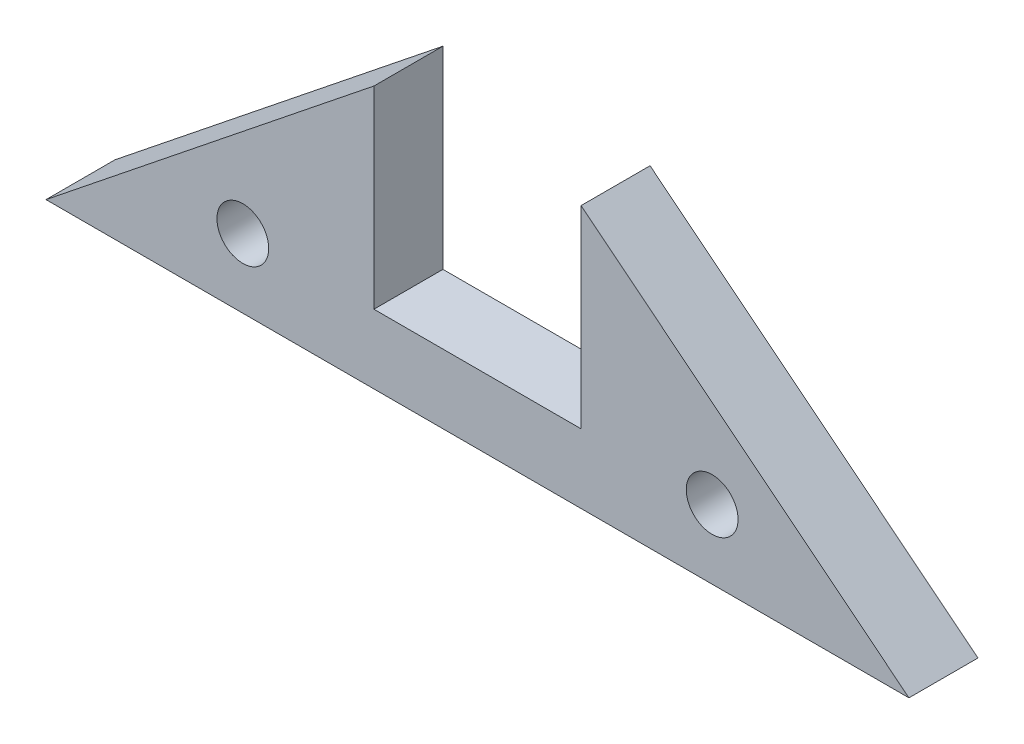
SolidWorks part; units mm, degrees
material "ABS"
ref_plane "Front" through (0, 0, 0) normal (0, 0, 1) x (1, 0, 0)
ref_plane "Top" through (0, 0, 0) normal (0, 1, 0) x (1, 0, 0)
ref_plane "Right" through (0, 0, 0) normal (1, 0, 0) x (0, 0, -1)
sketch "Sketch1" plane through (0, 0, 0) normal (0, 0, 1) x (1, 0, 0)
  line L0 (0, 0) -> (63.5, 0)
  line L1 (63.5, 0) -> (31.75, 25.4)
  line L2 (31.75, 25.4) -> (0, 0)
  point P6 (31.75, 0)
  dimension "D1" = 63.5
  dimension "D2" = 25.4
extrude "Boss-Extrude1" add sketch "Sketch1" along normal blind 5.08
sketch "Sketch2" plane through (0, 0, 5.08) normal (0, 0, 1) x (1, 0, 0)
  line L0 (0, 0) -> (63.5, 0) construction
  line L1 (31.75, 25.4) -> (0, 0) construction
  line L2 (63.5, 0) -> (31.75, 25.4) construction
  circle A0 centre (14.482, 5.08) radius 1.905
  circle A1 centre (49.018, 5.08) radius 1.905
  dimension "D1" = 3.81
  dimension "D2" = 5.08
  dimension "D3" = 5.08
  dimension "D4" = 5.08
extrude "Cut-Extrude1" cut sketch "Sketch2" against normal through all
ref_plane "Plane1" through (0, 5.08, 0) normal (0, -1, 0) x (-1, 0, 0)
sketch "Sketch5" plane through (0, 5.08, 0) normal (0, -1, 0) x (-1, 0, 0)
  line L0 (-16.387, -5.08) -> (-12.577, -5.08) construction
  line L1 (-24.13, 0) -> (-39.37, 0)
  line L2 (-24.13, 0) -> (-24.13, -5.08)
  line L3 (-24.13, -5.08) -> (-39.37, -5.08)
  line L4 (-39.37, 0) -> (-39.37, -5.08)
  line L5 (-12.577, 0) -> (-16.387, 0) construction
  line L6 (-47.625, -5.08) -> (-15.875, -5.08) construction
  line L7 (-31.75, -5.08) -> (0, -5.08) construction
  line L8 (-63.5, -5.08) -> (-31.75, -5.08) construction
  point P17 (-31.75, -5.08)
  dimension "D1" = 15.24
extrude "Cut-Extrude2" cut sketch "Sketch5" against normal through all
sketch "Sketch6" plane through (0, 0, 0) normal (0, -1, 0) x (-1, 0, 0)
  line L0 (0, 0) -> (-63.5, 0) construction
  point P0 (-31.75, 0)
